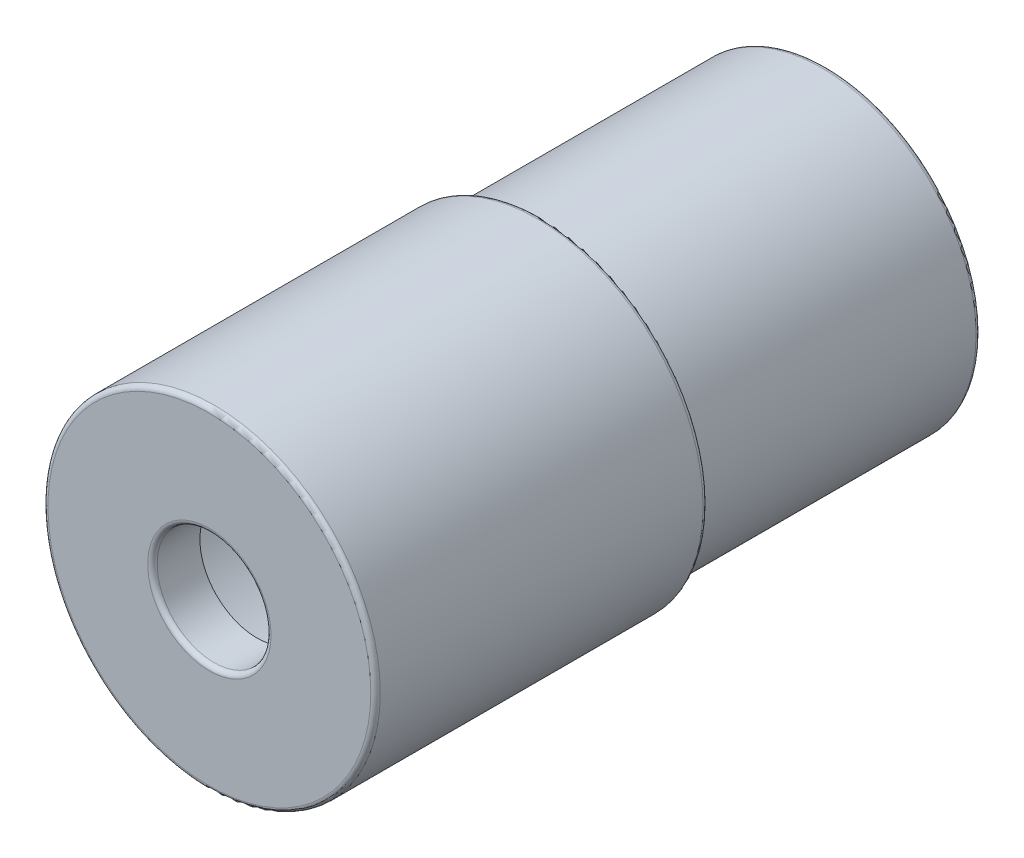
SolidWorks part; units mm, degrees
material "PVC 0.007 Plasticized"
ref_plane "Front Plane" through (0, 0, 0) normal (0, 0, 1) x (1, 0, 0)
ref_plane "Top Plane" through (0, 0, 0) normal (0, 1, 0) x (1, 0, 0)
ref_plane "Right Plane" through (0, 0, 0) normal (1, 0, 0) x (0, 0, -1)
sketch "Sketch1" plane through (0, 0, 0) normal (0, 0, 1) x (1, 0, 0)
  circle A0 centre (0, 0) radius 17.5
  circle A1 centre (0, 0) radius 15
  dimension "D1" = 35
  dimension "D2" = 30
extrude "Boss-Extrude1" add sketch "Sketch1" against normal blind 30
sketch "Sketch2" plane through (0, 0, -30) normal (0, 0, -1) x (-1, 0, 0)
  circle A3 centre (0, 0) radius 16.25
  circle A4 centre (0, 0) radius 15 construction
  circle A5 centre (0, 0) radius 15
  dimension "D1" = 32.5
extrude "Boss-Extrude2" add sketch "Sketch2" along normal blind 30 separate body
sketch "Sketch3" plane through (0, 0, 0) normal (0, 0, 1) x (1, 0, 0)
  circle A1 centre (0, 0) radius 17.5
  circle A2 centre (0, 0) radius 17.5
  dimension "D1" = 0
extrude "Boss-Extrude3" add sketch "Sketch3" along normal blind 5
sketch "Sketch4" plane through (0, 0, 5) normal (0, 0, 1) x (1, 0, 0)
  circle A0 centre (0, 0) radius 6
  dimension "D1" = 12
extrude "Cut-Extrude1" cut sketch "Sketch4" against normal blind 10
combine bodies "Combine1" operation type add bodies to combine 102 104
fillet "Fillet2" radius 0.5 1 edges at (-16.25, 0, -30)
fillet "Fillet3" radius 0.5 3 edges at (-15, 0, -60) (-16.25, 0, -60) (17.5, 0, -30)
fillet "Fillet4" radius 0.5 2 edges at (6, 0, 5) (17.5, 0, 5)
